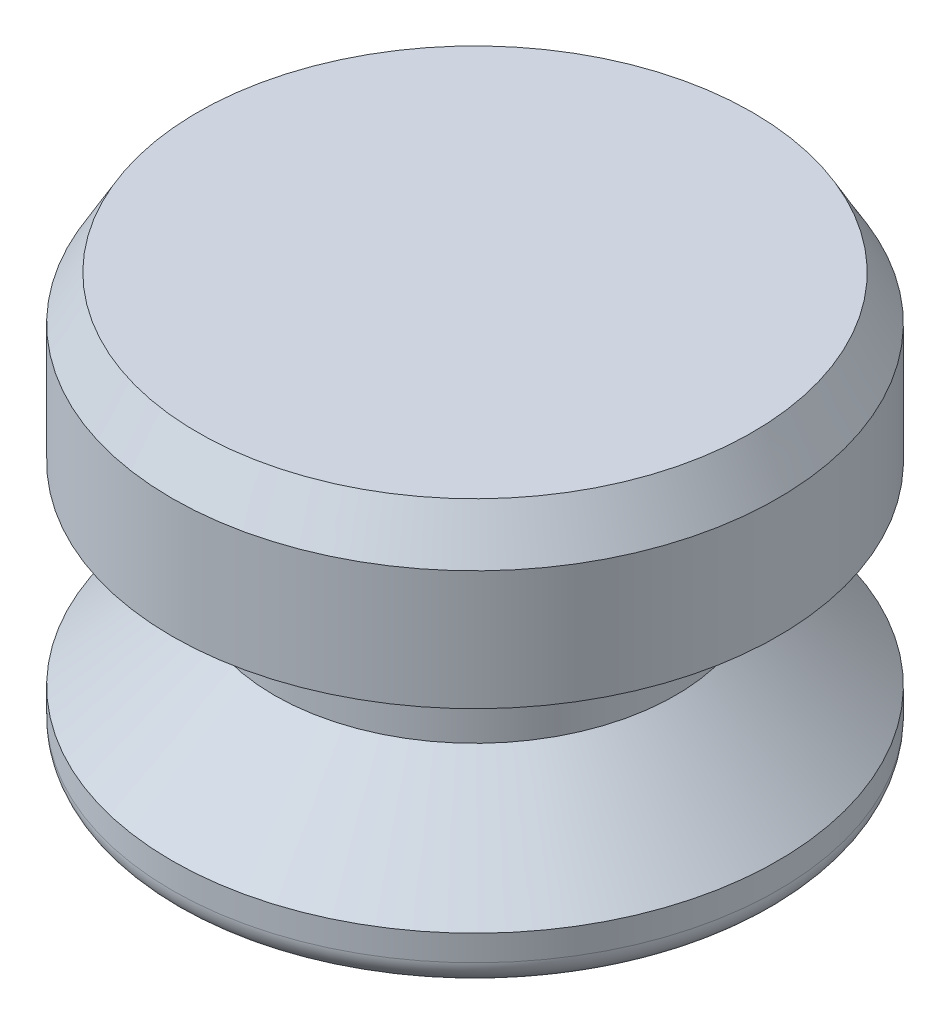
SolidWorks part; units mm, degrees
ref_plane "Front Plane" through (0, 0, 0) normal (0, 0, 1) x (1, 0, 0)
ref_plane "Top Plane" through (0, 0, 0) normal (0, 1, 0) x (1, 0, 0)
ref_plane "Right Plane" through (0, 0, 0) normal (1, 0, 0) x (0, 0, -1)
sketch "Sketch1" plane through (0, 0, 0) normal (0, 0, 1) x (1, 0, 0)
  line L0 (0, 0) -> (0, 12.7) construction
  line L1 (0, 0) -> (-9.398, 0)
  line L2 (-9.398, 0) -> (-9.398, 1.5875)
  line L4 (-6.223, 4.445) -> (-6.223, 7.62)
  line L5 (-6.223, 7.62) -> (-9.398, 7.62)
  line L6 (-9.398, 7.62) -> (-9.398, 12.7)
  line L7 (-9.398, 12.7) -> (0, 12.7)
  line L8 (-9.525, 16.6801) -> (-9.525, -9.6051) construction
  line L9 (0, 0) -> (0, 12.7)
  line L10 (-6.223, 4.445) -> (-9.398, 1.5875)
  dimension "D1" = 12.7
  dimension "D2" = 9.398
  dimension "D3" = 3.175
  dimension "D4" = 1.5875
  dimension "D5" = 9.525
  dimension "D6" = 6.223
  dimension "D7" = 7.62
revolve "Revolve1" add sketch "Sketch1" angle 360 about L9
fillet "Fillet1" radius 0.7937 1 edges at (0, 0, -9.398)
chamfer "Chamfer1" distance 0.7937 angle 60 1 edges at (0, 12.7, -9.398)
